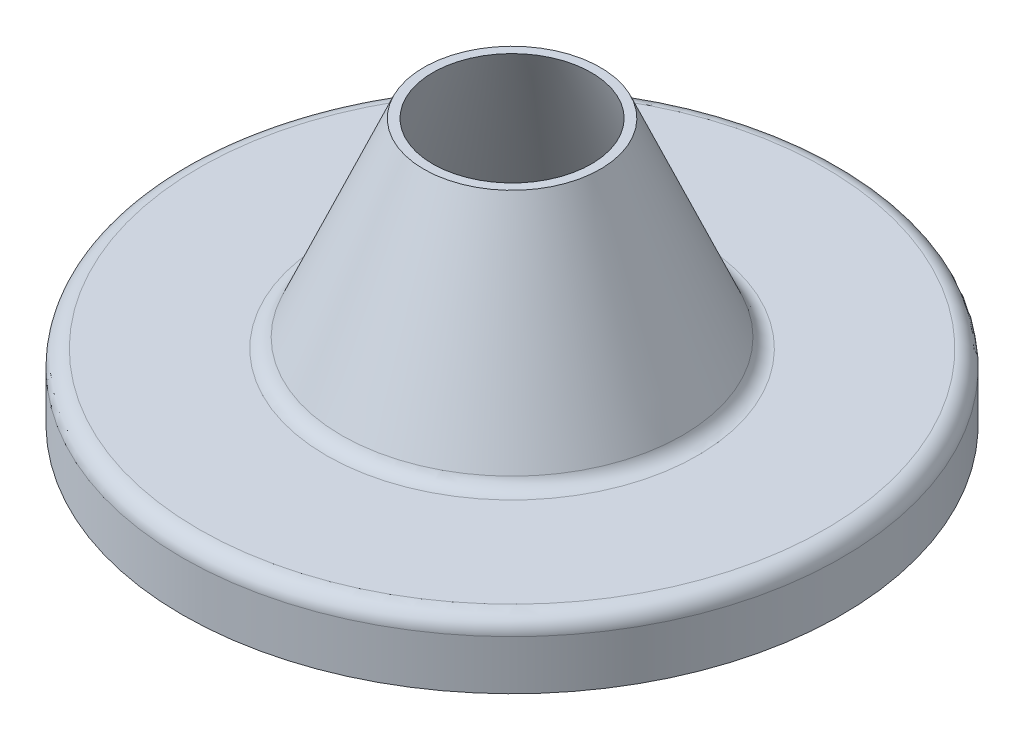
SolidWorks part; units mm, degrees
material "BUTYL"
ref_plane "Front Plane" through (0, 0, 0) normal (0, 0, 1) x (1, 0, 0)
ref_plane "Top Plane" through (0, 0, 0) normal (0, 1, 0) x (1, 0, 0)
ref_plane "Right Plane" through (0, 0, 0) normal (1, 0, 0) x (0, 0, -1)
sketch "Sketch1" plane through (0, 0, 0) normal (0, 0, 1) x (1, 0, 0)
  line L0 (0, 35.6402) -> (0, -28.6923) construction
  line L1 (4.875, -5.8266) -> (4.875, -5.2016)
  line L2 (5, -5.8266) -> (5, -5.0766)
  line L3 (4.625, -4.9516) -> (2.7321, -4.9516)
  line L4 (2.5027, -4.801) -> (1.2027, -1.801)
  line L5 (4.75, -4.8266) -> (2.8141, -4.8266)
  line L6 (2.5847, -4.676) -> (1.3389, -1.801)
  line L7 (1.2027, -1.801) -> (1.3389, -1.801)
  line L8 (4.875, -5.8266) -> (5, -5.8266)
  line L9 (5, -5.8266) -> (5, -4.8266) construction
  line L10 (2.65, -4.8266) -> (1.3174, -1.7513) construction
  line L11 (5, -4.8266) -> (2.65, -4.8266) construction
  line L12 (4.875, -5.8266) -> (4.875, -4.9516) construction
  line L13 (4.875, -4.9516) -> (2.5679, -4.9516) construction
  line L14 (2.5679, -4.9516) -> (1.2027, -1.801) construction
  arc A0 (5, -5.0766) -> (4.75, -4.8266) centre (4.75, -5.0766) ccw
  arc A1 (4.875, -5.2016) -> (4.625, -4.9516) centre (4.625, -5.2016) ccw
  arc A2 (2.7321, -4.9516) -> (2.5027, -4.801) centre (2.7321, -4.7016) cw
  arc A3 (2.8141, -4.8266) -> (2.5847, -4.676) centre (2.8141, -4.5766) cw
  point P15 (5, -4.8266)
  dimension "D1" = 0.25
  dimension "D7" = 0.25
  dimension "D8" = 0.25
  dimension "D2" = 10
  dimension "D3" = 1
  dimension "D4" = 0.125
  dimension "D5" = 0.1362
  dimension "D6" = 3.1333
  dimension "D9" = 1.9359
  dimension "D10" = 1.8929
  dimension "D11" = 1.2027
revolve "Revolve1" add sketch "Sketch1" angle 360 about L0
